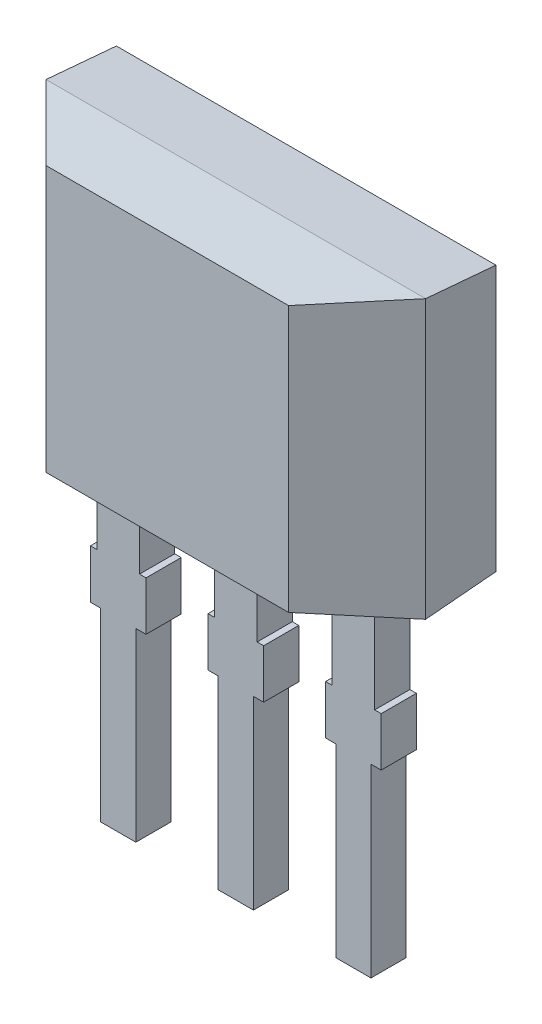
SolidWorks part; units mm, degrees
ref_plane "Front Plane" through (0, 0, 0) normal (0, 0, 1) x (1, 0, 0)
ref_plane "Top Plane" through (0, 0, 0) normal (0, 1, 0) x (1, 0, 0)
ref_plane "Right Plane" through (0, 0, 0) normal (1, 0, 0) x (0, 0, -1)
sketch "Sketch1" plane through (0, 0, 0) normal (0, 0, 1) x (1, 0, 0)
  line L1 (-2.05, 1.5) -> (2.05, 1.5)
  line L2 (-2.05, 1.5) -> (-2.05, -1.5)
  line L3 (-2.05, -1.5) -> (2.05, -1.5)
  line L4 (2.05, 1.5) -> (2.05, -1.5)
  dimension "D1" = 4.1
  dimension "D2" = 3
  dimension "D3" = 2.05
  dimension "D4" = 1.5
extrude "Extrude1" add sketch "Sketch1" along normal blind 0.74 draft 5 and the other way blind 0.76
sketch "Sketch2" plane through (0, 0, 0) normal (0, 1, 0) x (1, 0, 0)
  line L0 (-2.05, 0) -> (-1.023, -1.027)
  line L1 (-1.023, -1.027) -> (-2.05, -1.027)
  line L2 (-2.05, -1.027) -> (-2.05, 0)
  line L3 (2.05, 0) -> (1.0606, -0.9894)
  line L4 (1.0606, -0.9894) -> (2.05, -0.9894)
  line L5 (2.05, -0.9894) -> (2.05, 0)
extrude "Cut-Extrude1" cut sketch "Sketch2" against normal through all and the other way through all
sketch "Sketch3" plane through (0, 0, 0) normal (1, 0, 0) x (0, 0, -1)
  line L0 (0, 1.5) -> (1.2124, 1.3939)
  line L1 (1.2124, 1.3939) -> (0.76, 1.5)
  line L2 (0.76, 1.5) -> (0, 1.5)
  line L3 (0, -1.5) -> (1.1043, -1.5)
  line L4 (1.1043, -1.5) -> (1.1043, -1.4034)
  line L5 (1.1043, -1.4034) -> (0, -1.5)
extrude "Cut-Extrude2" cut sketch "Sketch3" against normal through all and the other way through all
sketch "Sketch4" plane through (0, 0, 0) normal (0, 0, 1) x (1, 0, 0)
  line L0 (1.46, -3.15) -> (1.57, -3.15)
  line L1 (-1.08, -3.15) -> (-0.97, -3.15)
  line L2 (0.23, -2.6218) -> (0.3, -2.6218)
  line L3 (-1.46, -5.15) -> (-1.27, -5.15)
  line L4 (-1.04, -2.6218) -> (-0.97, -2.6218)
  line L5 (-1.27, -5.15) -> (-1.08, -5.15)
  line L6 (0.19, -3.15) -> (0.3, -3.15)
  line L7 (-0.19, -3.15) -> (-0.19, -5.15)
  line L8 (-0.19, -5.15) -> (0, -5.15)
  line L9 (0.19, -3.15) -> (0.19, -5.15)
  line L10 (1.5, -2.6218) -> (1.57, -2.6218)
  line L11 (1.08, -3.15) -> (1.08, -5.15)
  line L12 (1.08, -5.15) -> (1.27, -5.15)
  line L13 (1.46, -3.15) -> (1.46, -5.15)
  line L14 (-1.5, -0.7875) -> (-1.04, -0.7875)
  line L15 (-1.5, -0.7875) -> (-1.5, -2.6218)
  line L16 (-1.08, -3.15) -> (-1.08, -5.15)
  line L17 (-1.04, -0.7875) -> (-1.04, -2.6218)
  line L18 (-0.23, -0.7875) -> (0.23, -0.7875)
  line L19 (-0.23, -0.7875) -> (-0.23, -2.6218)
  line L20 (-2.05, -1.5) -> (2.05, -1.5) construction
  line L21 (0.23, -0.7875) -> (0.23, -2.6218)
  line L22 (1.04, -0.7875) -> (1.5, -0.7875)
  line L23 (1.04, -0.7875) -> (1.04, -2.6218)
  line L25 (1.5, -0.7875) -> (1.5, -2.6218)
  line L26 (0, -5.15) -> (0.19, -5.15)
  line L27 (1.27, -5.15) -> (1.46, -5.15)
  line L29 (-1.57, -2.6218) -> (-1.5, -2.6218)
  line L30 (-1.57, -2.6218) -> (-1.57, -3.15)
  line L31 (-1.57, -3.15) -> (-1.46, -3.15)
  line L32 (-0.97, -2.6218) -> (-0.97, -3.15)
  line L33 (-0.3, -2.6218) -> (-0.23, -2.6218)
  line L34 (-0.3, -2.6218) -> (-0.3, -3.15)
  line L35 (-0.3, -3.15) -> (-0.19, -3.15)
  line L36 (0.3, -2.6218) -> (0.3, -3.15)
  line L37 (0.97, -2.6218) -> (1.04, -2.6218)
  line L38 (0.97, -2.6218) -> (0.97, -3.15)
  line L39 (0.97, -3.15) -> (1.08, -3.15)
  line L40 (1.57, -2.6218) -> (1.57, -3.15)
  line L41 (-1.46, -3.15) -> (-1.46, -5.15)
  dimension "D2" = 0.5282
  dimension "D3" = 1.65
  dimension "D4" = 0.19
  dimension "D5" = 2.54
  dimension "D6" = 1.27
  dimension "D7" = 0.3
  dimension "D8" = 0.3
  dimension "D9" = 0.3
  dimension "D10" = 0.3
  dimension "D11" = 0.3
  dimension "D12" = 0.3
  dimension "D13" = 0.46
  dimension "D14" = 0.46
  dimension "D15" = 0.46
  dimension "D16" = 0.23
  dimension "D17" = 0.23
  dimension "D18" = 0.23
  dimension "D19" = 2
extrude "Extrude2" add sketch "Sketch4" against normal blind 0.38
sketch "Sketch5" plane through (0, 0, 0) normal (0, 0, 1) x (1, 0, 0)
  circle A0 centre (0, -0.5) radius 3
  dimension "D1" = 6
  dimension "D2" = 0.5
ref_plane "Board Plane" through (0, -3.2, 0) normal (0, 1, 0) x (-1, 0, 0)
sketch "Component_Outline" plane through (0, -3.2, 0) normal (0, 1, 0) x (-1, 0, 0)
  line L0 (2.05, -0.76) -> (2.05, 0)
  line L1 (2.05, 0) -> (1.31, 0.74)
  line L2 (1.31, 0.74) -> (-1.31, 0.74)
  line L3 (-1.31, 0.74) -> (-2.05, 0)
  line L4 (-2.05, 0) -> (-2.05, -0.76)
  line L5 (-2.05, -0.76) -> (2.05, -0.76)
  point P6 (0, 0)
